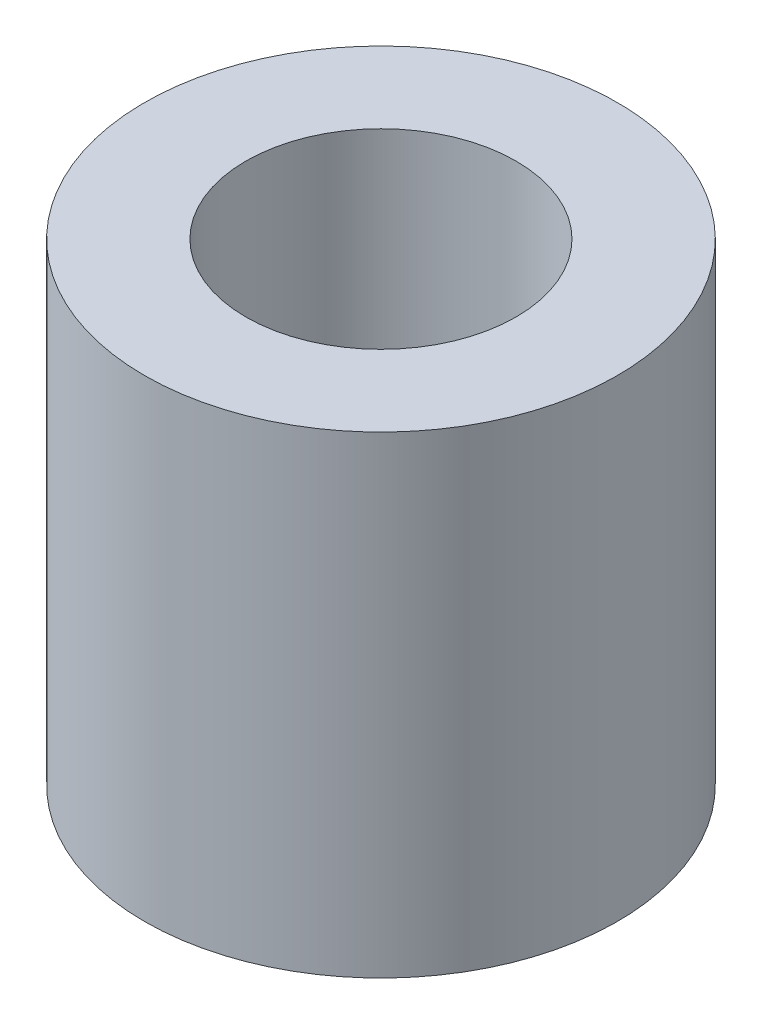
SolidWorks part; units mm, degrees
ref_plane "Front Plane" through (0, 0, 0) normal (0, 0, 1) x (1, 0, 0)
ref_plane "Top Plane" through (0, 0, 0) normal (0, 1, 0) x (1, 0, 0)
ref_plane "Right Plane" through (0, 0, 0) normal (1, 0, 0) x (0, 0, -1)
sketch "Sketch1" plane through (0, 0, 0) normal (0, 1, 0) x (1, 0, 0)
  circle A0 centre (0, 0) radius 2
  circle A1 centre (0, 0) radius 3.5
  dimension "D1" = 4
  dimension "D2" = 1.5
extrude "Boss-Extrude1" add sketch "Sketch1" along normal mid plane 7
